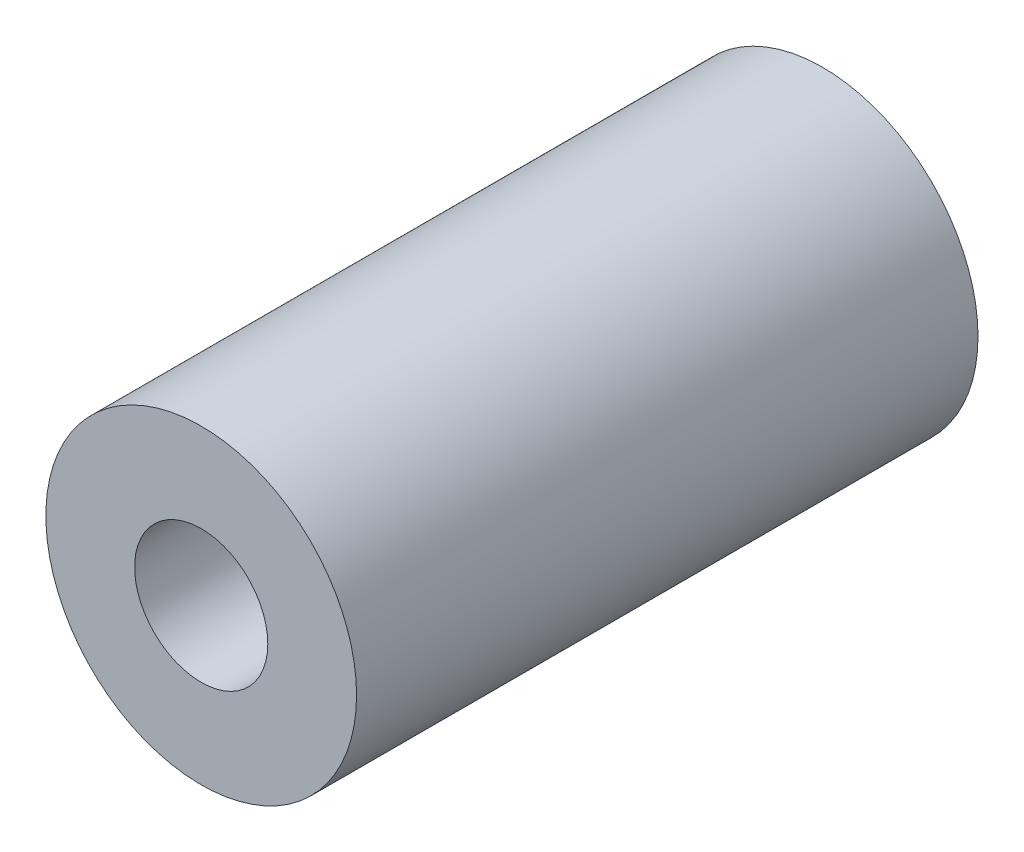
SolidWorks part; units mm, degrees
material "6061-T6 (SS)"
ref_plane "Front Plane" through (0, 0, 0) normal (0, 0, 1) x (1, 0, 0)
ref_plane "Top Plane" through (0, 0, 0) normal (0, 1, 0) x (1, 0, 0)
ref_plane "Right Plane" through (0, 0, 0) normal (1, 0, 0) x (0, 0, -1)
sketch "Sketch1" plane through (0, 0, 0) normal (0, 0, 1) x (1, 0, 0)
  circle A0 centre (0, 0) radius 11.1125
  circle A1 centre (0, 0) radius 4.7625
  dimension "D1" = 22.225
  dimension "D2" = 9.525
extrude "Boss-Extrude1" add sketch "Sketch1" along normal blind 44.45
